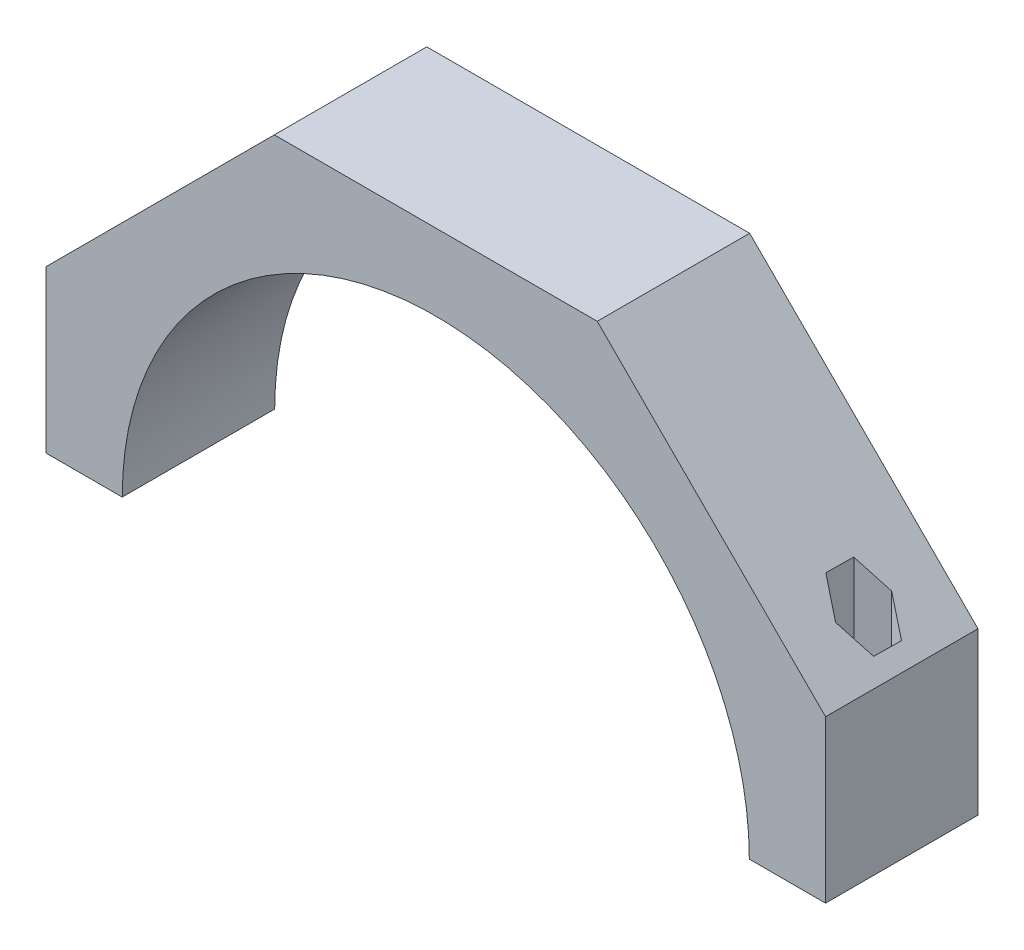
SolidWorks part; units mm, degrees
ref_plane "Front Plane" through (0, 0, 0) normal (0, 0, 1) x (1, 0, 0)
ref_plane "Top Plane" through (0, 0, 0) normal (0, 1, 0) x (1, 0, 0)
ref_plane "Right Plane" through (0, 0, 0) normal (1, 0, 0) x (0, 0, -1)
sketch "Sketch1" plane through (0, 0, 0) normal (0, 0, 1) x (1, 0, 0)
  line L0 (-78.359, 0) -> (-97.409, 0)
  line L1 (-97.409, 0) -> (-97.409, 40.3481)
  line L2 (-40.3481, 97.409) -> (40.3481, 97.409)
  line L3 (-97.409, 40.3481) -> (-40.3481, 97.409)
  line L4 (-31.833, 78.359) -> (33.3017, 78.359) construction
  line L5 (97.409, 40.3481) -> (40.3481, 97.409)
  line L6 (97.409, 0) -> (97.409, 40.3481)
  line L7 (78.359, 0) -> (97.409, 0)
  line L8 (70.05, 40.7663) -> (39.2881, 71.5283) construction
  line L9 (-71.3801, 39.4363) -> (-43.2728, 67.5435) construction
  arc A0 (78.359, 0) -> (-78.359, 0) centre (0, 0) ccw
  dimension "D1" = 19.05
  dimension "D2" = 135
  dimension "D3" = 156.718
  dimension "D4" = 19.05
  dimension "D5" = 19.05
  dimension "D6" = 19.05
extrude "Boss-Extrude1" add sketch "Sketch1" along normal mid plane 38.1
sketch "Sketch2" plane through (0, 0, 0) normal (0, -1, 0) x (1, 0, 0)
  line L0 (0, 0) -> (81.8011, 0)
  line L3 (97.409, 19.05) -> (97.409, -19.05) construction
  line L4 (0, 18.0843) -> (0, -14.477)
  line L6 (78.359, -19.05) -> (97.409, -19.05) construction
  circle A0 centre (87.884, 0) radius 3.429
  circle A1 centre (-87.884, 0) radius 3.429
  point P3 (90.2508, 0)
  point P4 (0, 0)
  point P7 (0, 0)
  point P15 (0, 0)
  point P18 (59.055, 0)
  dimension "D1" = 6.858
  dimension "D2" = 9.525
  dimension "D3" = 19.05
extrude "Cut-Extrude2" cut sketch "Sketch2" against normal through all
ref_plane "Plane1" through (0, 19.05, 0) normal (0, -1, 0) x (-1, 0, 0)
sketch "Sketch4" plane through (0, 19.05, 0) normal (0, -1, 0) x (-1, 0, 0)
  line L1 (-93.9254, 3.429) -> (-93.8743, -3.5175)
  line L2 (-93.8743, -3.5175) -> (-87.8329, -6.9465)
  line L3 (-87.8329, -6.9465) -> (-81.8426, -3.429)
  line L4 (-81.8426, -3.429) -> (-81.8937, 3.5175)
  line L5 (-81.8937, 3.5175) -> (-87.9351, 6.9465)
  line L6 (-87.9351, 6.9465) -> (-93.9254, 3.429)
  line L7 (-78.359, -19.05) -> (-97.409, -19.05) construction
  line L8 (-97.409, -19.05) -> (-97.409, 19.05) construction
  circle A0 centre (87.884, 0) radius 5.6772
  circle A1 centre (-87.884, 0) radius 6.016 construction
  point P4 (-87.884, 0)
  point P16 (0, 0)
  dimension "D1" = 6.9465
  dimension "D2" = 9.525
  dimension "D3" = 19.05
extrude "Cut-Extrude3" cut sketch "Sketch4" against normal through all
